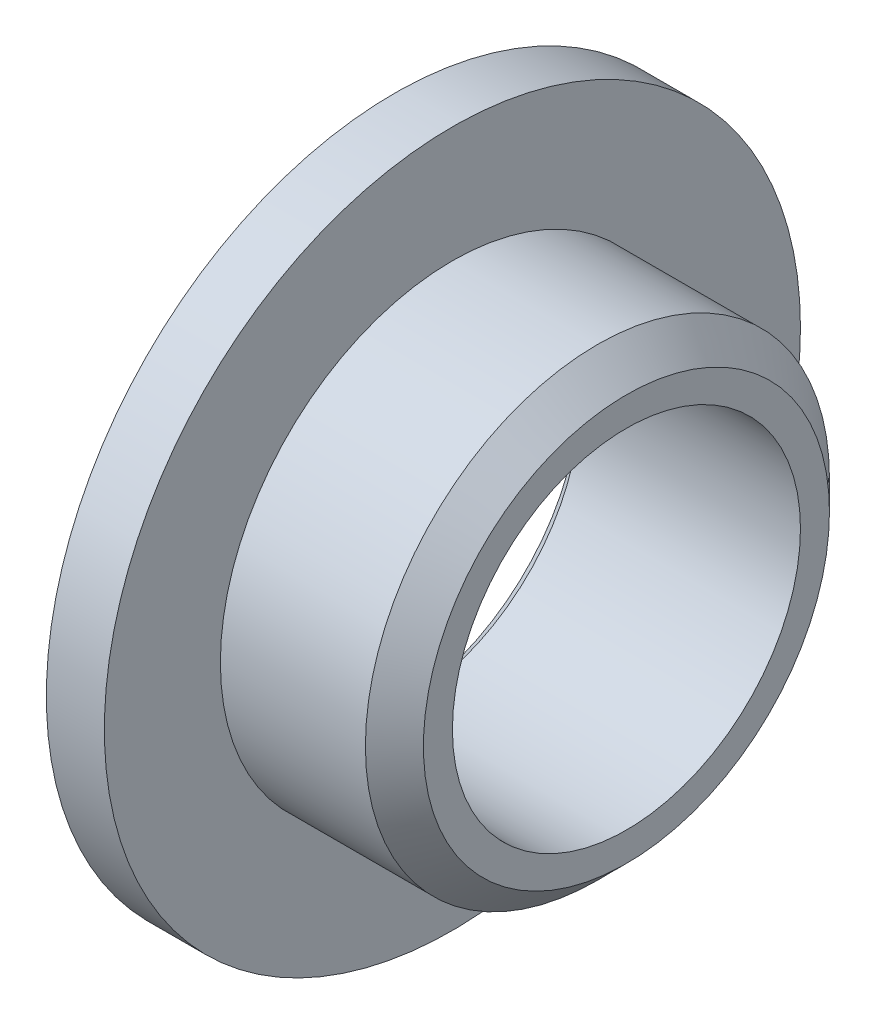
SolidWorks part; units mm, degrees
ref_plane "Piano frontale" through (0, 0, 0) normal (0, 0, 1) x (1, 0, 0)
ref_plane "Piano superiore" through (0, 0, 0) normal (0, 1, 0) x (1, 0, 0)
ref_plane "Piano destro" through (0, 0, 0) normal (1, 0, 0) x (0, 0, -1)
sketch "Schizzo1" plane through (0, 0, 0) normal (0, 0, 1) x (1, 0, 0)
  line L0 (0, 6) -> (0, 3.2)
  line L1 (0, 3.2) -> (0.2, 3)
  line L2 (0.2, 3) -> (4, 3)
  line L3 (4, 3) -> (4, 3.5)
  line L4 (4, 3.5) -> (3.5, 4)
  line L5 (3.5, 4) -> (1, 4)
  line L6 (1, 4) -> (1, 6)
  line L7 (1, 6) -> (0, 6)
  line L8 (0, 0) -> (4, 0) construction
  dimension "D1" = 4
  dimension "D2" = 3
  dimension "D3" = 1
  dimension "D4" = 1
  dimension "D5" = 6
  dimension "D6" = 2.5
  dimension "D7" = 0.5
revolve "Rivoluzione1" add sketch "Schizzo1" angle 360 about L8
